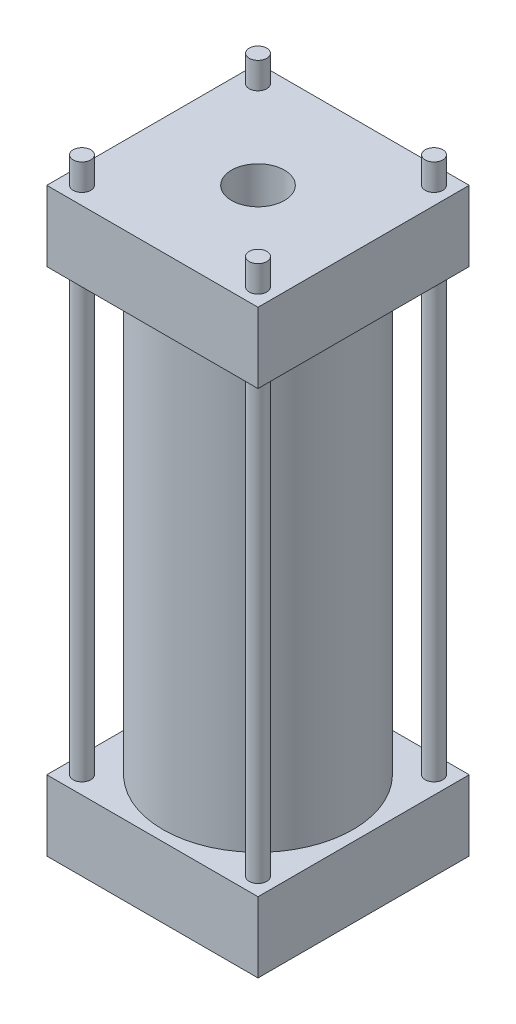
SolidWorks part; units mm, degrees
material "3004-O, Rod (SS)"
ref_plane "Front Plane" through (0, 0, 0) normal (0, 0, 1) x (1, 0, 0)
ref_plane "Top Plane" through (0, 0, 0) normal (0, 1, 0) x (1, 0, 0)
ref_plane "Right Plane" through (0, 0, 0) normal (1, 0, 0) x (0, 0, -1)
sketch "Sketch1" plane through (0, 0, 0) normal (0, 1, 0) x (1, 0, 0)
  circle A0 centre (0, 0) radius 50
  circle A1 centre (0, 0) radius 54
  dimension "D1" = 4
extrude "Boss-Extrude1" add sketch "Sketch1" along normal blind 250
sketch "Sketch2" plane through (0, 0, 0) normal (0, -1, 0) x (1, 0, 0)
  line L1 (60, 60) -> (-60, 60)
  line L2 (60, 60) -> (60, -60)
  line L3 (60, -60) -> (-60, -60)
  line L4 (-60, 60) -> (-60, -60)
  line L5 (60, 60) -> (-60, -60) construction
  line L6 (60, -60) -> (-60, 60) construction
  point P1 (0, 0)
  dimension "D1" = 120
  dimension "D2" = 120
extrude "Boss-Extrude2" add sketch "Sketch2" along normal blind 40
sketch "Sketch3" plane through (0, 250, 0) normal (0, 1, 0) x (1, 0, 0)
  line L4 (-60, 60) -> (-60, -60)
  line L5 (-60, -60) -> (60, -60)
  line L6 (60, -60) -> (60, 60)
  line L7 (60, 60) -> (-60, 60)
  line L8 (-60, 60) -> (-60, -60)
  line L9 (-60, -60) -> (60, -60)
  line L10 (60, -60) -> (60, 60)
  line L11 (60, 60) -> (-60, 60)
  dimension "D1" = 0
extrude "Boss-Extrude3" add sketch "Sketch3" along normal blind 40
sketch "Sketch4" plane through (0, 290, 0) normal (0, 1, 0) x (1, 0, 0)
  circle A0 centre (0, 0) radius 15
extrude "Cut-Extrude1" cut sketch "Sketch4" against normal up to next
sketch "Sketch5" plane through (0, 290, 0) normal (0, 1, 0) x (1, 0, 0)
  line L0 (-60, 60) -> (-60, -60) construction
  line L1 (60, 60) -> (-60, 60) construction
  circle A0 centre (-50, 50) radius 5
  dimension "D3" = 10
  dimension "D1" = 10
  dimension "D2" = 10
extrude "Boss-Extrude4" add sketch "Sketch5" along normal blind 15 and the other way blind 295
pattern_linear "LPattern1" count 2 spacing 100 along (1, 0, 0) count 2 spacing 100 along (0, 0, 1) of "Boss-Extrude4"
ref_point "Point1"
